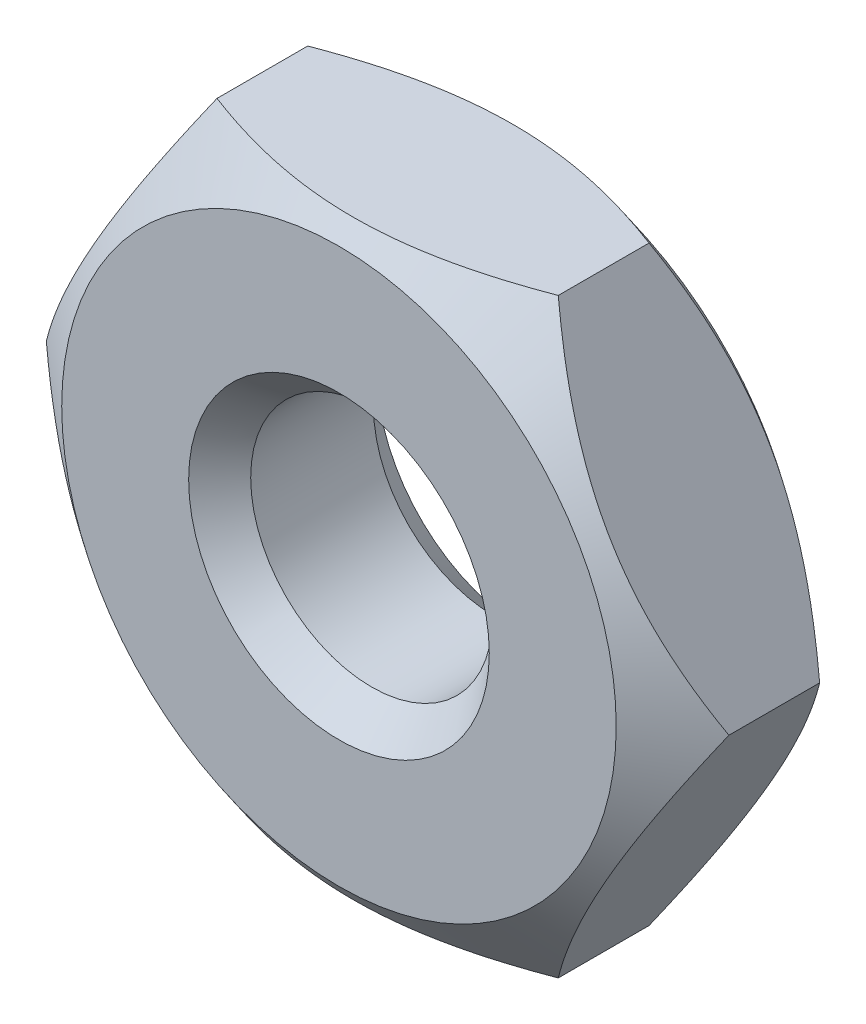
SolidWorks part; units mm, degrees
material "ASTM A36 Steel"
ref_plane "Front Plane" through (0, 0, 0) normal (0, 0, 1) x (1, 0, 0)
ref_plane "Top Plane" through (0, 0, 0) normal (0, 1, 0) x (1, 0, 0)
ref_plane "Right Plane" through (0, 0, 0) normal (1, 0, 0) x (0, 0, -1)
sketch "Sketch1" plane through (0, 0, 0) normal (0, 0, 1) x (1, 0, 0)
  line L1 (3.1754, 0) -> (1.5877, 2.75)
  line L2 (1.5877, 2.75) -> (-1.5877, 2.75)
  line L3 (-1.5877, 2.75) -> (-3.1754, 0)
  line L4 (-3.1754, 0) -> (-1.5877, -2.75)
  line L5 (-1.5877, -2.75) -> (1.5877, -2.75)
  line L6 (1.5877, -2.75) -> (3.1754, 0)
  circle A0 centre (0, 0) radius 2.75 construction
  circle A1 centre (0, 0) radius 1.125
  dimension "D1" = 2.25
extrude "Extrude1" add sketch "Sketch1" along normal mid plane 1.75
sketch "Sketch2" plane through (0, 0, 0) normal (0, 1, 0) x (1, 0, 0)
  line L0 (0, 0.875) -> (0, -0.875) construction
  line L1 (1.5877, 0.875) -> (-1.5877, 0.875) construction
  line L2 (3.1754, 0.875) -> (3.1754, 0.4222)
  line L3 (3.1754, -0.875) -> (3.1754, 0.875) construction
  line L4 (3.1754, 0.4222) -> (2.5797, 0.875)
  line L5 (3.1754, 0.875) -> (1.5877, 0.875) construction
  line L6 (2.5797, 0.875) -> (3.1754, 0.875)
  line L7 (3.1754, -0.875) -> (3.1754, -0.4222)
  line L8 (3.1754, -0.4222) -> (2.5797, -0.875)
  line L9 (3.1754, -0.875) -> (1.5877, -0.875) construction
  line L10 (2.5797, -0.875) -> (3.1754, -0.875)
  line L11 (1.0424, 0.875) -> (1.3987, 0.875)
  line L12 (1.125, 0.875) -> (-1.125, 0.875) construction
  line L13 (-1.5877, 0.875) -> (1.5877, 0.875) construction
  line L14 (1.3987, 0.875) -> (1.0424, 0.4797)
  line L15 (1.0424, 0.4797) -> (1.0424, 0.875)
  line L16 (1.0424, -0.875) -> (1.3987, -0.875)
  line L17 (-1.125, -0.875) -> (1.125, -0.875) construction
  line L18 (-1.5877, -0.875) -> (1.5877, -0.875) construction
  line L19 (1.3987, -0.875) -> (1.0424, -0.4797)
  line L20 (1.0424, -0.4797) -> (1.0424, -0.875)
revolve "Cut-Revolve1" cut sketch "Sketch2" angle 360 about L0
